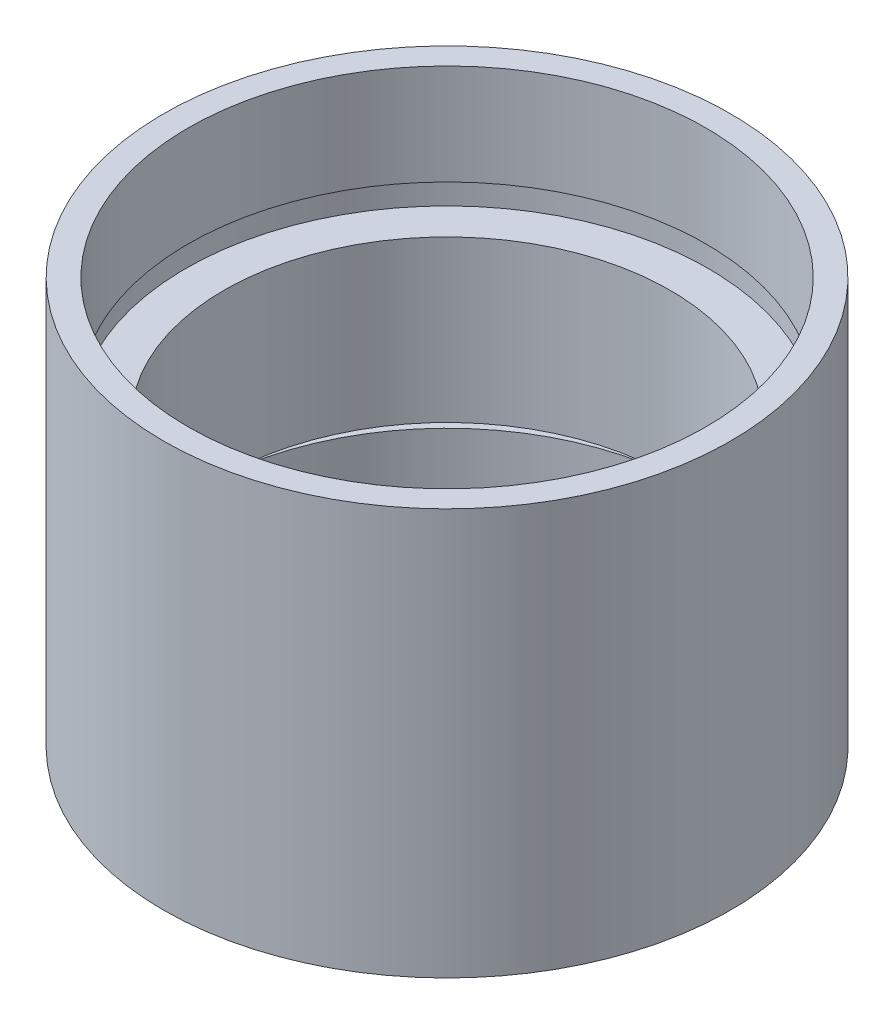
SolidWorks part; units mm, degrees
ref_plane "前视基准面" through (0, 0, 0) normal (0, 0, 1) x (1, 0, 0)
ref_plane "上视基准面" through (0, 0, 0) normal (0, 1, 0) x (1, 0, 0)
ref_plane "右视基准面" through (0, 0, 0) normal (1, 0, 0) x (0, 0, -1)
sketch "草图1" plane through (0, 0, 0) normal (0, 0, 1) x (1, 0, 0)
  line L0 (0, 161.3762) -> (0, 0) construction
  line L1 (141.7365, 0) -> (-131.7984, 0) construction
  line L2 (11.1, 0) -> (11.1, 4.5)
  line L3 (11.7, 4.5) -> (11.7, 5.5)
  line L4 (11.1, 4.5) -> (11.7, 4.5)
  line L5 (10, 5.5) -> (10, 12.7)
  line L6 (11.7, 5.5) -> (10, 5.5)
  line L7 (12.7, 0) -> (12.7, 18.2)
  line L8 (11.1, 0) -> (12.7, 0)
  line L9 (11.6, 18.2) -> (11.6, 13.7)
  line L10 (11.6, 18.2) -> (12.7, 18.2)
  line L11 (11.7, 13.7) -> (11.7, 12.7)
  line L12 (11.6, 13.7) -> (11.7, 13.7)
  line L13 (10, 12.7) -> (11.7, 12.7)
  point P15 (11.6, 15.95)
  dimension "D1" = 11.1
  dimension "D2" = 4.5
  dimension "D3" = 11.7
  dimension "D4" = 10
  dimension "D5" = 12.7
  dimension "D6" = 11.6
  dimension "D7" = 4.5
  dimension "D8" = 11.7
  dimension "D9" = 5.5
  dimension "D10" = 1
  dimension "D11" = 12.7
revolve "旋转1" add sketch "草图1" angle 360 about L0
cosmetic thread "装饰螺纹线1" parameters "D2"=23.2
cosmetic thread "装饰螺纹线2" parameters "D2"=21
cosmetic thread "装饰螺纹线3" parameters "D2"=23.21
